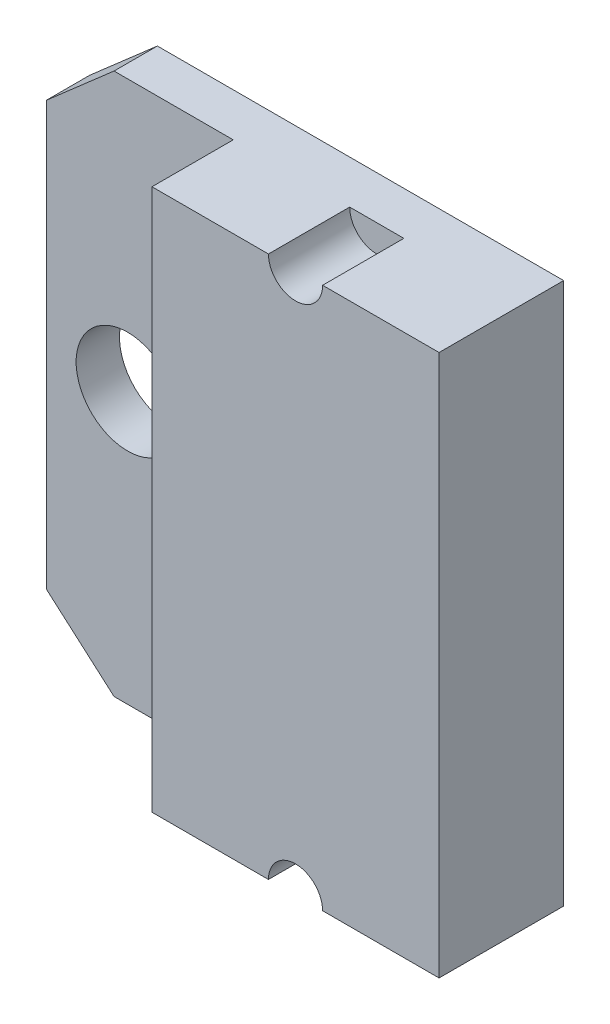
SolidWorks part; units mm, degrees
ref_plane "Front Plane" through (0, 0, 0) normal (0, 0, 1) x (1, 0, 0)
ref_plane "Top Plane" through (0, 0, 0) normal (0, 1, 0) x (1, 0, 0)
ref_plane "Right Plane" through (0, 0, 0) normal (1, 0, 0) x (0, 0, -1)
sketch "Sketch1" plane through (0, 0, 0) normal (0, 0, 1) x (1, 0, 0)
  line L0 (-7.5, 6.465) -> (-5, 8.65)
  line L1 (10, -11.35) -> (-5, -11.35)
  line L2 (10, -11.35) -> (10, 8.65)
  line L3 (10, 8.65) -> (-5, 8.65)
  line L4 (-7.5, -9.165) -> (-7.5, 6.465)
  line L5 (10, -11.35) -> (-6.4808, 7.3557) construction
  line L6 (10, 8.65) -> (-9.0396, -7.8193) construction
  line L7 (-7.5, -1.35) -> (10, -1.35) construction
  line L8 (-7.5, -9.165) -> (-5, -11.35)
  line L9 (-7.5, -1.35) -> (1.25, -1.35) construction
  circle A0 centre (-4.5, -1.35) radius 1.9
  point P0 (0, 0)
  dimension "D3" = 17.5
  dimension "D2" = 3.8
  dimension "D1" = 20
  dimension "D4" = 15
  dimension "D5" = 14.5
extrude "Boss-Extrude1" add sketch "Sketch1" along normal blind 1.6
sketch "Sketch2" plane through (0, 0, 1.6) normal (0, 0, 1) x (1, 0, 0)
  line L1 (10, 8.65) -> (-0.6, 8.65)
  line L2 (10, 8.65) -> (10, -11.35)
  line L3 (10, -11.35) -> (-0.6, -11.35)
  line L4 (-0.6, 8.65) -> (-0.6, -11.35)
  dimension "D1" = 20
  dimension "D2" = 10.6
sketch "Sketch3" plane through (0, 0, 1.6) normal (0, 0, 1) x (1, 0, 0)
extrude "Boss-Extrude2" add sketch "Sketch2" along normal blind 3
sketch "Sketch4" plane through (0, 0, 4.6) normal (0, 0, 1) x (1, 0, 0)
  line L0 (-0.6, -11.35) -> (10, -11.35) construction
  line L1 (-0.6, -1.35) -> (10, -1.35) construction
  line L2 (-0.6, 8.65) -> (-0.6, -11.35) construction
  line L3 (10, -11.35) -> (10, 8.65) construction
  circle A0 centre (4.7, -11.35) radius 1
  circle A1 centre (4.7, 8.65) radius 1
  dimension "D1" = 2
extrude "Cut-Extrude1" cut sketch "Sketch4" against normal blind 3
sketch "Sketch5" plane through (10, 0, 0) normal (1, 0, 0) x (0, 0, -1)
  line L0 (-2.3, 8.65) -> (-2.3, -11.35) construction
  line L1 (-4.6, 8.65) -> (0, 8.65) construction
  line L2 (-4.6, -11.35) -> (0, -11.35) construction
